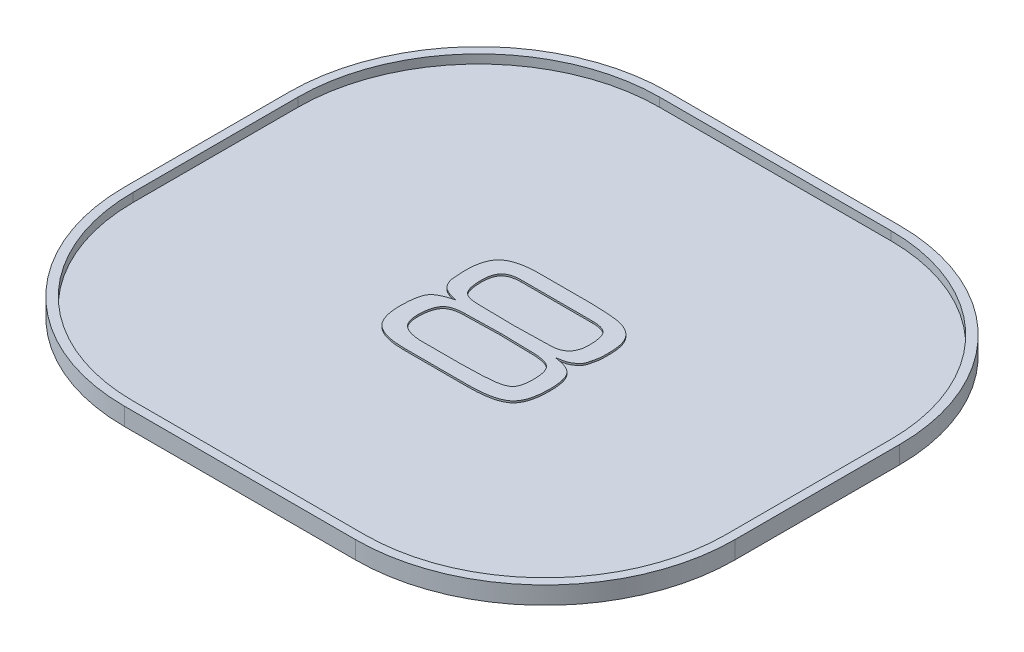
SolidWorks part; units mm, degrees
ref_plane "Front Plane" through (0, 0, 0) normal (0, 0, 1) x (1, 0, 0)
ref_plane "Top Plane" through (0, 0, 0) normal (0, 1, 0) x (1, 0, 0)
ref_plane "Right Plane" through (0, 0, 0) normal (1, 0, 0) x (0, 0, -1)
sketch "Sketch1" plane through (0, 0, 0) normal (0, 1, 0) x (1, 0, 0)
  line L0 (-1.3539, -2.9989) -> (1.2696, -2.9989)
  line L1 (3.4196, -0.8489) -> (3.4196, 1.0211)
  line L2 (1.2696, 3.1711) -> (-1.3539, 3.1711)
  line L3 (-3.5039, 1.0211) -> (-3.5039, -0.8489)
  arc A0 (-3.5039, -0.8489) -> (-1.3539, -2.9989) centre (-1.3539, -0.8489) ccw
  arc A1 (1.2696, -2.9989) -> (3.4196, -0.8489) centre (1.2696, -0.8489) ccw
  arc A2 (3.4196, 1.0211) -> (1.2696, 3.1711) centre (1.2696, 1.0211) ccw
  arc A3 (-1.3539, 3.1711) -> (-3.5039, 1.0211) centre (-1.3539, 1.0211) ccw
extrude "Boss-Extrude1" add sketch "Sketch1" along normal blind 0.2
shell "Shell1" thickness 0.1
sketch "Sketch2" plane through (0, 0.1, 0) normal (0, 1, 0) x (1, 0, 0)
  text T0 "8" font "Eurostile Extended" height 1.5
extrude "Boss-Extrude2" add sketch "Sketch2" along normal blind 0.02
